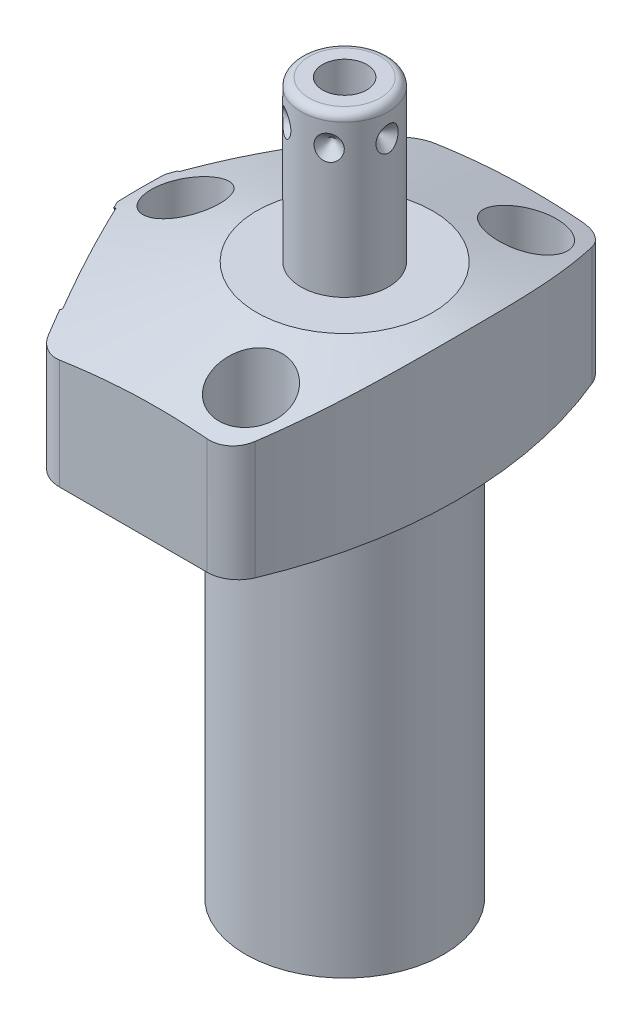
SolidWorks part; units mm, degrees
material "Alloy Steel"
ref_plane "Front Plane" through (0, 0, 0) normal (0, 0, 1) x (1, 0, 0)
ref_plane "Top Plane" through (0, 0, 0) normal (0, 1, 0) x (1, 0, 0)
ref_plane "Right Plane" through (0, 0, 0) normal (1, 0, 0) x (0, 0, -1)
ref_plane "Plane1" through (0, 0, 0) normal (0, 0, 1) x (0, -1, 0)
sketch "Sketch1" plane through (0, 0, 0) normal (0, 0, 1) x (0, -1, 0)
  line L0 (0, 28.575) -> (-19.05, 28.575)
  line L1 (-19.05, 28.575) -> (-19.05, 0)
  line L2 (-19.05, 0) -> (50.8, 0)
  line L3 (50.8, 0) -> (50.8, 12.573)
  line L4 (50.8, 12.573) -> (0, 12.573)
  line L5 (0, 12.573) -> (0, 28.575)
  line L6 (-22.5425, 0) -> (54.2925, 0) construction
  dimension "D1" = 69.85
  dimension "D2" = 19.05
  dimension "D3" = 25.146
  dimension "D4" = 57.15
revolve "Revolve1" add sketch "Sketch1" angle 360 about L6
ref_plane "Plane2" through (0, 0, 0) normal (0, -1, 0) x (0, 0, -1)
sketch "Sketch2" plane through (0, 0, 0) normal (0, -1, 0) x (0, 0, -1)
  line L0 (23.8125, -15.7954) -> (23.8125, 15.7954)
  line L2 (-23.8125, 15.7954) -> (-23.8125, -15.7954)
  line L3 (0, -18.0139) -> (0, 30.7935) construction
  arc A0 (23.8125, -15.7954) -> (23.8125, 15.7954) centre (0, 0) ccw
  circle A1 centre (0, 0) radius 28.575
  arc A2 (-23.8125, 15.7954) -> (-23.8125, -15.7954) centre (0, 0) ccw
  point P4 (0, 0)
  dimension "D1" = 47.625
  dimension "D2" = 0
extrude "Cut-Extrude1" cut sketch "Sketch2" against normal up to next
ref_plane "Plane3" through (0, 0, 0) normal (0, -1, 0) x (-1, 0, 0)
sketch "Sketch3" plane through (0, 0, 0) normal (0, -1, 0) x (-1, 0, 0)
  line L0 (14.7539, 23.8125) -> (27.4152, 0)
  line L1 (27.4152, 0) -> (14.7539, -23.8125)
  line L2 (-24.5787, -13.0687) -> (45.9515, 24.4329) construction
  line L3 (0, 0) -> (35.175, 0) construction
  line L4 (15.7954, -23.8125) -> (-15.7954, -23.8125) construction
  line L5 (-15.7954, 23.8125) -> (15.7954, 23.8125) construction
  line L6 (15.7954, -23.8125) -> (14.7539, -23.8125)
  line L7 (14.7539, 23.8125) -> (15.7954, 23.8125)
  arc A0 (15.7954, -23.8125) -> (15.7954, 23.8125) centre (0, 0) ccw construction
  arc A1 (15.7954, -23.8125) -> (15.7954, 23.8125) centre (0, 0) ccw
  dimension "D1" = 28
  dimension "D2" = 24.2062
extrude "Cut-Extrude2" cut sketch "Sketch3" against normal up to next
ref_plane "Plane4" through (0, 0, 0) normal (0, -1, 0) x (-1, 0, 0)
sketch "S2D0002" plane through (0, 0, 0) normal (0, -1, 0) x (-1, 0, 0)
  line L0 (25.8064, 53.3791) -> (25.8064, -53.3791)
  arc A0 (25.8064, 53.3791) -> (25.8064, -53.3791) centre (41.275, 0) ccw
  dimension "D1" = 55.5752
  dimension "D2" = 15.4686
  dimension "D3" = 41.275
extrude "Cut-Extrude3" cut sketch "S2D0002" against normal blind 26.035 flip side to cut
fillet "Fillet1" radius 3.9624 4 edges at (8.9402, 9.525, 23.8125) (-14.7539, 9.525, 23.8125) (-14.7539, 9.525, -23.8125) (8.9402, 9.525, -23.8125)
ref_plane "Plane5" through (0, 0, 0) normal (0, 0, 1) x (1, 0, 0)
sketch "Sketch5" plane through (0, 0, 0) normal (0, 0, 1) x (1, 0, 0)
  line L0 (-11.176, 19.05) -> (-44.45, 8.2386)
  line L1 (0, 5.9984) -> (0, 19.6715) construction
  line L2 (-15.8716, 19.05) -> (-25.8064, 19.05) construction
  line L3 (-11.176, 19.05) -> (-44.45, 19.05)
  line L4 (-44.45, 19.05) -> (-44.45, 8.2386)
  dimension "D1" = 22.352
  dimension "D2" = 18
  dimension "D3" = 44.45
revolve "Cut-Revolve1" cut sketch "Sketch5" angle 360 about L1
ref_plane "Plane6" through (-21.1485, 7.9502, -11.2449) normal (0, 1, 0) x (0.4695, 0, -0.8829)
sketch "Sketch6" plane through (-21.1485, 7.9502, -11.2449) normal (0, 1, 0) x (0.4695, 0, -0.8829)
  line L0 (0, 0) -> (4.5466, 0)
  line L1 (4.5466, 0) -> (4.1066, -2.0701)
  line L2 (4.1066, -2.0701) -> (3.4544, -2.7223)
  line L3 (3.4544, -2.7223) -> (3.4544, -12.192)
  line L4 (3.4544, -12.192) -> (0, -12.192)
  line L5 (0, -12.192) -> (0, 0)
  line L6 (0, -12.8016) -> (0, 0.6096) construction
  dimension "D1" = 12.192
revolve "Cut-Revolve2" cut sketch "Sketch6" angle 360 about L6
ref_plane "Plane7" through (-21.1485, 7.9502, 11.2449) normal (0, 1, 0) x (-0.4695, 0, -0.8829)
sketch "Sketch7" plane through (-21.1485, 7.9502, 11.2449) normal (0, 1, 0) x (-0.4695, 0, -0.8829)
  line L0 (0, 0) -> (4.5466, 0)
  line L1 (4.5466, 0) -> (4.1066, -2.0701)
  line L2 (4.1066, -2.0701) -> (3.4544, -2.7223)
  line L3 (3.4544, -2.7223) -> (3.4544, -12.192)
  line L4 (3.4544, -12.192) -> (0, -12.192)
  line L5 (0, -12.192) -> (0, 0)
  line L6 (0, -12.8016) -> (0, 0.6096) construction
  dimension "D1" = 12.192
revolve "Cut-Revolve3" cut sketch "Sketch7" angle 360 about L6
ref_plane "Plane8" through (-11.1252, 2.667, -15.875) normal (0, 0, 1) x (-1, 0, 0)
sketch "Sketch17" plane through (-21.3728, 0, 11.3641) normal (-0.8829, 0, 0.4695) x (0.4695, 0, 0.8829)
  circle A0 centre (0, 7.9502) radius 10.4775
  dimension "D1" = 20.955
extrude "Cut-Extrude4" cut sketch "Sketch17" against normal blind 0.254
sketch "Sketch18" plane through (-21.3728, 0, -11.3641) normal (-0.8829, 0, -0.4695) x (-0.4695, 0, 0.8829)
  circle A0 centre (0, 7.9502) radius 10.4775
  dimension "D1" = 20.955
extrude "Cut-Extrude5" cut sketch "Sketch18" against normal blind 0.254
sketch "Sketch8" plane through (-11.1252, 2.667, -15.875) normal (0, 0, 1) x (-1, 0, 0)
  line L0 (0, 0) -> (4.5466, 0)
  line L1 (4.5466, 0) -> (4.1066, -2.0701)
  line L2 (4.1066, -2.0701) -> (3.4544, -2.7223)
  line L3 (3.4544, -2.7223) -> (3.4544, -11.684)
  line L4 (3.4544, -11.684) -> (0, -11.684)
  line L5 (0, -11.684) -> (0, 0)
  line L6 (0, -12.2682) -> (0, 0.5842) construction
  dimension "D1" = 11.684
revolve "Cut-Revolve4" cut sketch "Sketch8" angle 360 about L6
ref_plane "Plane9" through (-11.1252, 2.667, 15.875) normal (0, 0, 1) x (-1, 0, 0)
sketch "Sketch9" plane through (-11.1252, 2.667, 15.875) normal (0, 0, 1) x (-1, 0, 0)
  line L0 (0, 0) -> (4.5466, 0)
  line L1 (4.5466, 0) -> (4.1066, -2.0701)
  line L2 (4.1066, -2.0701) -> (3.4544, -2.7223)
  line L3 (3.4544, -2.7223) -> (3.4544, -11.684)
  line L4 (3.4544, -11.684) -> (0, -11.684)
  line L5 (0, -11.684) -> (0, 0)
  line L6 (0, -12.2682) -> (0, 0.5842) construction
  dimension "D1" = 11.684
revolve "Cut-Revolve5" cut sketch "Sketch9" angle 360 about L6
ref_plane "Plane10" through (0, 0, 0) normal (1, 0, 0) x (0, 0, -1)
sketch "Sketch10" plane through (0, 0, 0) normal (1, 0, 0) x (0, 0, -1)
  line L0 (0, 19.05) -> (-5.5562, 19.05)
  line L1 (-5.5562, 19.05) -> (-5.5562, 38.3032)
  line L2 (-4.5402, 39.3192) -> (0, 39.3192)
  line L3 (0, 39.3192) -> (0, 19.05)
  line L4 (0, 18.0365) -> (0, 44.824) construction
  line L5 (11.176, 19.05) -> (-11.176, 19.05) construction
  line L6 (-21.374, 0) -> (21.374, 0) construction
  arc A0 (-4.5402, 39.3192) -> (-5.5562, 38.3032) centre (-4.5402, 38.3032) ccw
  dimension "D3" = 1.016
  dimension "D1" = 11.1125
  dimension "D2" = 39.3192
revolve "Revolve2" add sketch "Sketch10" angle 360 about L4
sketch "Sketch19" plane through (0, 0, 0) normal (0, -1, 0) x (1, 0, 0)
  circle A0 centre (-11.1252, -15.875) radius 5.5626
  circle A1 centre (-11.1252, 15.875) radius 5.5626
  dimension "D1" = 11.1252
extrude "Cut-Extrude6" cut sketch "Sketch19" against normal blind 2.667
ref_plane "Plane11" through (2.8067, 39.3192, 0) normal (0, 0, 1) x (1, 0, 0)
sketch "S2D0001" plane through (2.8067, 39.3192, 0) normal (0, 0, 1) x (1, 0, 0)
  line L0 (0, 0) -> (0, -10.16)
  line L1 (0, -10.16) -> (-2.8067, -11.8464)
  line L2 (0, 0) -> (-2.8067, 0)
  line L3 (-2.8067, 0) -> (-2.8067, -11.8464)
  line L4 (-2.8067, -17.5667) -> (-2.8067, 0.5923) construction
  line L5 (1.7335, 0) -> (-7.3469, 0) construction
  dimension "D1" = 5.6134
  dimension "D2" = 10.16
  dimension "D3" = 59
revolve "Cut-Revolve6" cut sketch "S2D0001" angle 360 about L4
ref_plane "Plane12" through (-21.1485, 0, -11.2449) normal (0.8829, 0, 0.4695) x (0.4695, 0, -0.8829)
sketch "Sketch12" plane through (-21.1485, 0, -11.2449) normal (0.8829, 0, 0.4695) x (0.4695, 0, -0.8829)
  circle A0 centre (0, 7.9502) radius 4.8006
  circle A1 centre (0, 7.9502) radius 3.4544 construction
  dimension "D1" = 9.6012
extrude "Extrude1" add sketch "Sketch12" against normal blind 1.651
sketch "Sketch13" plane through (0, 0, 0) normal (0, -1, 0) x (1, 0, 0)
  circle A0 centre (-11.1252, -15.875) radius 4.8006
  circle A1 centre (-11.1252, -15.875) radius 5.5626 construction
  dimension "D1" = 9.6012
ref_plane "Plane13" through (-11.1252, 2.667, -15.875) normal (0, 1, 0) x (-1, 0, 0)
extrude "Extrude2" add sketch "Sketch13" against normal up to surface
ref_plane "Plane14" through (-11.1252, 0, 15.875) normal (1, 0, 0) x (0, 0, -1)
sketch "Sketch14" plane through (-11.1252, 0, 15.875) normal (1, 0, 0) x (0, 0, -1)
  line L0 (5.461, 2.667) -> (5.461, 0.9398)
  line L1 (5.461, 0.9398) -> (5.3016, 0.9398)
  line L2 (2.667, 0.4318) -> (2.667, 0.127)
  line L3 (2.667, 0.127) -> (1.5875, 0.127)
  line L4 (1.5875, 0.127) -> (1.5875, 10.6172)
  line L5 (1.5875, 10.6172) -> (3.2512, 10.6172)
  line L6 (3.2512, 10.6172) -> (3.2512, 2.667)
  line L7 (3.2512, 2.667) -> (5.461, 2.667)
  line L8 (3.175, 0.9398) -> (3.8424, 0.9398)
  line L9 (0, -1.0109) -> (0, 11.1709) construction
  line L10 (-3.4544, 14.351) -> (-3.4544, 5.3893) construction
  line L11 (3.4544, 5.3893) -> (3.4544, 14.351) construction
  line L12 (-5.499, 0) -> (37.249, 0) construction
  arc A0 (3.175, 0.9398) -> (2.667, 0.4318) centre (3.175, 0.4318) ccw
  arc A1 (3.8424, 0.9398) -> (5.3016, 0.9398) centre (4.572, 0.4318) ccw
  dimension "D5" = 0.508
  dimension "D9" = 0.889
  dimension "D1" = 2.54
  dimension "D2" = 7.9502
  dimension "D3" = 3.175
  dimension "D4" = 0.127
  dimension "D6" = 5.334
  dimension "D7" = 0.3048
  dimension "D8" = 0.3048
  dimension "D10" = 9.144
  dimension "D11" = 10.922
  dimension "D12" = 6.5024
revolve "Revolve3" add sketch "Sketch14" angle 360 about L9
ref_plane "Plane15" through (-5.5562, 35.3568, 0) normal (0, 0, 1) x (0, 1, 0)
sketch "Sketch15" plane through (-5.5562, 35.3568, 0) normal (0, 0, 1) x (0, 1, 0)
  line L0 (0, 0) -> (1.5875, 0)
  line L1 (1.5875, 0) -> (0, -1.5875)
  line L2 (0, 0) -> (0, -1.5875)
  line L3 (0, -3.7018) -> (0, 0.0794) construction
  line L4 (2.9464, 0) -> (-16.3068, 0) construction
  line L5 (3.9624, -10.0965) -> (3.9624, -1.016) construction
  dimension "D1" = 3.9624
  dimension "D2" = 3.175
  dimension "D3" = 45
ref_plane "Plane16" through (5.5562, 35.3568, 0) normal (0, 0, 1) x (0, -1, 0)
revolve "Cut-Revolve7" cut sketch "Sketch15" angle 360 about L3
pattern_circular "CirPattern1" count 6 over 360 about axis through (0, 18.0365, 0) along (0, -1, 0) of "Cut-Revolve7"
hole_wizard "Hole1" positions "Sketch21" profile "Sketch20" legacy end condition up to next
sketch "Sketch21" plane through (0, 19.05, 0) normal (0, 1, 0) x (-1, 0, 0)
  line L0 (0, 0) -> (31.1465, 0) construction
  line L1 (0, 0) -> (0, 26.4037) construction
  point P0 (-5.5626, -17.4498)
  point P9 (20.193, 0)
  point P13 (-5.5626, 17.4498)
  dimension "D1" = 5.5626
  dimension "D2" = 17.4498
  dimension "D3" = 20.193
sketch "Sketch20" plane through (5.5626, 19.05, -17.4498) normal (1, 0, 0) x (0, 0, 1)
  line L0 (0, 0) -> (0, 19.05)
  line L1 (0, 19.05) -> (2.7813, 19.05)
  line L2 (2.7813, 19.05) -> (2.7813, 11.0998)
  line L3 (2.7813, 11.0998) -> (4.3561, 11.0998)
  line L4 (4.3561, 11.0998) -> (4.3561, 0)
  line L5 (4.3561, 0) -> (0, 0)
  line L6 (0, 110) -> (0, -10) construction
  dimension "Diameter" = 5.5626
  dimension "Depth" = 19.05
  dimension "C-Bore Diameter" = 8.7122
  dimension "C-Bore Depth" = 11.0998
